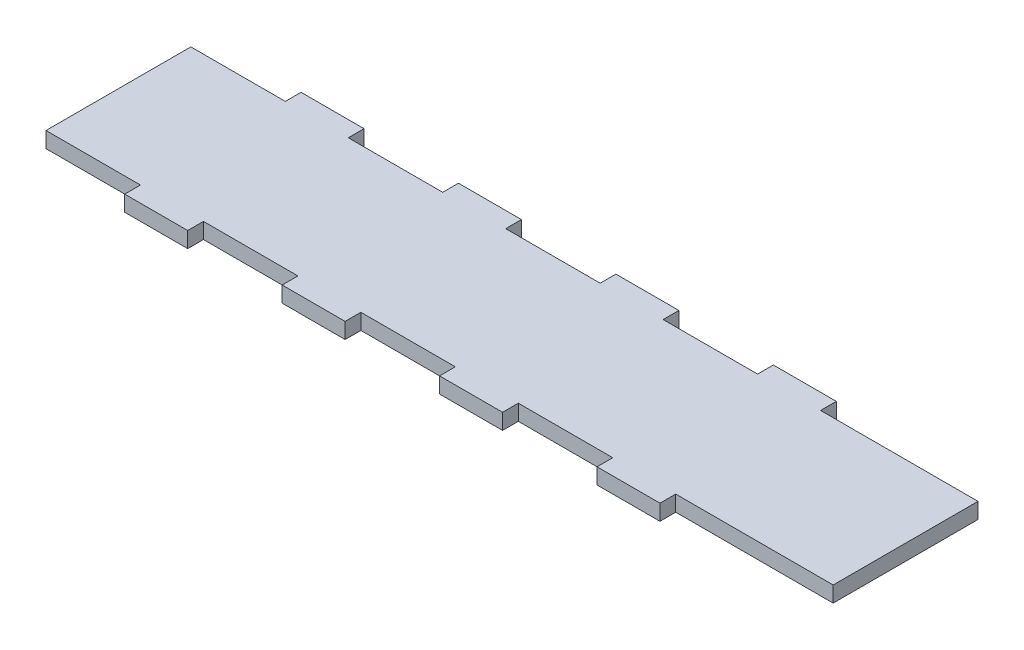
SolidWorks part; units mm, degrees
ref_plane "Front Plane" through (0, 0, 0) normal (0, 0, 1) x (1, 0, 0)
ref_plane "Top Plane" through (0, 0, 0) normal (0, 1, 0) x (1, 0, 0)
ref_plane "Right Plane" through (0, 0, 0) normal (1, 0, 0) x (0, 0, -1)
sketch "Sketch1" plane through (0, 0, 0) normal (0, 1, 0) x (1, 0, 0)
  line L0 (0, 0) -> (112.6687, 0) construction
  line L1 (-79.375, 17.78) -> (79.375, 17.78)
  line L2 (-79.375, 17.78) -> (-79.375, -17.78)
  line L3 (-79.375, -17.78) -> (79.375, -17.78)
  line L4 (79.375, 17.78) -> (79.375, -17.78)
  line L5 (112.6687, 0) -> (0, 0) construction
  line L6 (0, 0) -> (0, 39.063) construction
  dimension "D1" = 35.56
  dimension "D2" = 158.75
  dimension "D3" = 17.78
  dimension "D4" = 79.375
extrude "Extrude1" add sketch "Sketch1" along normal blind 3.175
sketch "Sketch3" plane through (0, 3.175, 0) normal (0, 1, 0) x (1, 0, 0)
  line L1 (47.625, -14.605) -> (66.675, -14.605)
  line L2 (47.625, -17.78) -> (47.625, -14.605)
  line L4 (-79.375, 17.78) -> (-60.325, 17.78)
  line L5 (-79.375, 17.78) -> (-79.375, 14.605)
  line L6 (-79.375, 14.605) -> (-60.325, 14.605)
  line L7 (-60.325, 17.78) -> (-60.325, 14.605)
  line L8 (47.625, -17.78) -> (66.675, -17.78)
  line L9 (66.675, 17.78) -> (79.375, 17.78)
  line L10 (79.375, 17.78) -> (79.375, 14.605)
  line L11 (79.375, 14.605) -> (66.675, 14.605)
  line L12 (66.675, -14.605) -> (79.375, -14.605)
  line L13 (79.375, -14.605) -> (79.375, -17.78)
  line L14 (79.375, -17.78) -> (66.675, -17.78)
  line L17 (-79.375, 0) -> (79.375, 0) construction
  line L18 (-79.375, 17.78) -> (-79.375, -17.78) construction
  line L19 (79.375, -17.78) -> (79.375, 17.78) construction
  line L20 (34.925, -14.605) -> (34.925, -17.78)
  line L21 (15.875, -14.605) -> (34.925, -14.605)
  line L22 (15.875, -17.78) -> (15.875, -14.605)
  line L23 (15.875, -17.78) -> (34.925, -17.78)
  line L24 (3.175, -17.78) -> (3.175, -14.605)
  line L25 (-15.875, -14.605) -> (3.175, -14.605)
  line L26 (-15.875, -17.78) -> (-15.875, -14.605)
  line L27 (-15.875, -17.78) -> (3.175, -17.78)
  line L28 (-28.575, -17.78) -> (-28.575, -14.605)
  line L29 (-60.325, -17.78) -> (-60.325, -14.605)
  line L30 (-79.375, -14.605) -> (-60.325, -14.605)
  line L31 (-79.375, -17.78) -> (-79.375, -14.605)
  line L32 (-79.375, -17.78) -> (-60.325, -17.78)
  line L33 (-47.625, -14.605) -> (-28.575, -14.605)
  line L34 (-47.625, -17.78) -> (-47.625, -14.605)
  line L35 (-47.625, -17.78) -> (-28.575, -17.78)
  line L36 (-47.625, 17.78) -> (-28.575, 17.78)
  line L37 (-47.625, 17.78) -> (-47.625, 14.605)
  line L39 (-47.625, 14.605) -> (-28.575, 14.605)
  line L40 (-28.575, 17.78) -> (-28.575, 14.605)
  line L41 (-15.875, 17.78) -> (3.175, 17.78)
  line L42 (-15.875, 17.78) -> (-15.875, 14.605)
  line L43 (-15.875, 14.605) -> (3.175, 14.605)
  line L44 (3.175, 17.78) -> (3.175, 14.605)
  line L45 (15.875, 17.78) -> (34.925, 17.78)
  line L46 (15.875, 17.78) -> (15.875, 14.605)
  line L47 (15.875, 14.605) -> (34.925, 14.605)
  line L48 (34.925, 17.78) -> (34.925, 14.605)
  line L49 (47.625, 17.78) -> (66.675, 17.78)
  line L50 (47.625, 17.78) -> (47.625, 14.605)
  line L51 (47.625, 14.605) -> (66.675, 14.605)
  line L87 (66.675, 17.78) -> (66.675, 14.605) [skipped]
  dimension "D1" = 3.175
  dimension "D2" = 5
  dimension "D4" = 19.05
extrude "Cut-Extrude1" cut sketch "Sketch3" against normal through all
equation "\"D3@Sketch1\" = \"D1@Sketch1\"/2"
equation "\"D4@Sketch1\"=\"D2@Sketch1\"/2"
